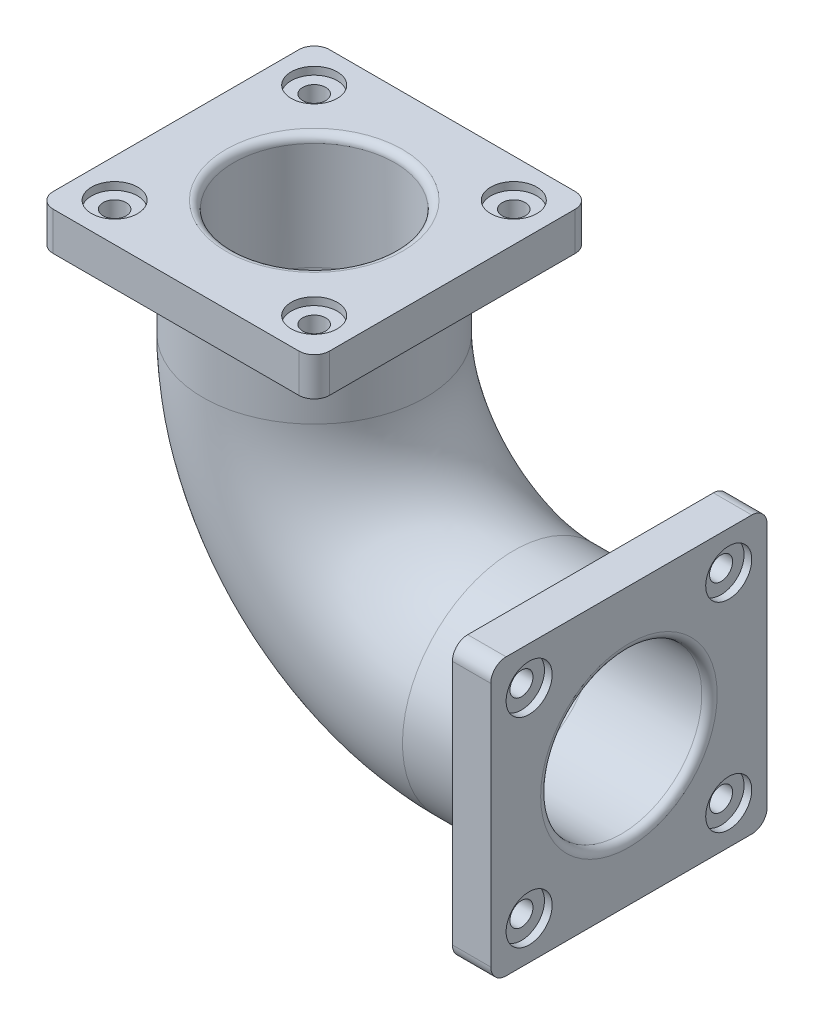
SolidWorks part; units mm, degrees
material "1060 Alloy"
ref_plane "Front Plane" through (0, 0, 0) normal (0, 0, 1) x (1, 0, 0)
ref_plane "Top Plane" through (0, 0, 0) normal (0, 1, 0) x (1, 0, 0)
ref_plane "Right Plane" through (0, 0, 0) normal (1, 0, 0) x (0, 0, -1)
sketch "Sketch4" plane through (0, 0, 0) normal (0, 0, 1) x (1, 0, 0)
  line L0 (150, 0) -> (0, 0)
  line L1 (-260, 260) -> (-260, 410)
  arc A0 (0, 0) -> (-260, 260) centre (0, 260) cw
  dimension "D3" = 260
  dimension "D1" = 150
  dimension "D2" = 150
ref_plane "Plane1" through (0, 410, 0) normal (0, 1, 0) x (1, 0, 0)
sketch "Sketch6" plane through (0, 410, 0) normal (0, 1, 0) x (1, 0, 0)
  line L0 (-260, 0) -> (0, 0) construction
  circle A0 centre (-260, 0) radius 105
  circle A1 centre (-260, 0) radius 145
  dimension "D1" = 290
  dimension "D2" = 210
sweep "Sweep1" add profiles "Sketch6" path "Sketch4"
sketch "Sketch9" plane through (150, 0, 0) normal (1, 0, 0) x (0, 0, -1)
  line L0 (-180, 0) -> (180, 0) construction
  line L1 (-180, 180) -> (180, 180)
  line L2 (-180, 180) -> (-180, -180)
  line L3 (-180, -180) -> (180, -180)
  line L4 (180, 180) -> (180, -180)
  line L5 (0, 180) -> (0, -180) construction
  circle A2 centre (0, 0) radius 105
  circle A3 centre (-130, 130) radius 15
  circle A6 centre (130, 130) radius 15
  circle A7 centre (130, -130) radius 15
  circle A8 centre (-130, -130) radius 15
  dimension "D5" = 210
  dimension "D6" = 50
  dimension "D9" = 30
  dimension "D1" = 360
  dimension "D2" = 360
  dimension "D3" = 180
  dimension "D4" = 180
  dimension "D7" = 50
extrude "Boss-Extrude1" add sketch "Sketch9" against normal blind 50
fillet "Fillet1" radius 20 4 edges at (125, -180, 180) (125, -180, -180) (125, 180, -180) (125, 180, 180)
sketch "Sketch11" plane through (150, 0, 0) normal (1, 0, 0) x (0, 0, -1)
  line L0 (-180, 0) -> (180, 0) construction
  line L1 (-180, 160) -> (-180, -160) construction
  line L2 (180, -160) -> (180, 160) construction
  line L3 (0, 180) -> (0, -180) construction
  line L4 (160, 180) -> (-160, 180) construction
  line L5 (-160, -180) -> (160, -180) construction
  circle A0 centre (-130, 130) radius 30
  circle A1 centre (130, 130) radius 30
  circle A2 centre (130, -130) radius 30
  circle A3 centre (-130, -130) radius 30
  dimension "D1" = 60
extrude "Cut-Extrude1" cut sketch "Sketch11" against normal blind 10
fillet "Fillet2" radius 10 1 edges at (150, 0, 105)
ref_plane "Plane4" through (150, 0, 0) normal (1, 0, 0) x (0, 0, -1)
ref_plane "Plane5" through (-130, 130, 0) normal (0.7071, -0.7071, 0) x (-0.7071, -0.7071, 0)
mirror "Mirror4" about plane through (-130, 130, 0) normal (0.7071, -0.7071, 0) of "Cut-Extrude1", "Fillet1", "Boss-Extrude1"
fillet "Fillet3" radius 10 1 edges at (-260, 410, 105)
fillet "Fillet4" radius 10 2 edges at (100, 0, -145) (-405, 360, 0)
